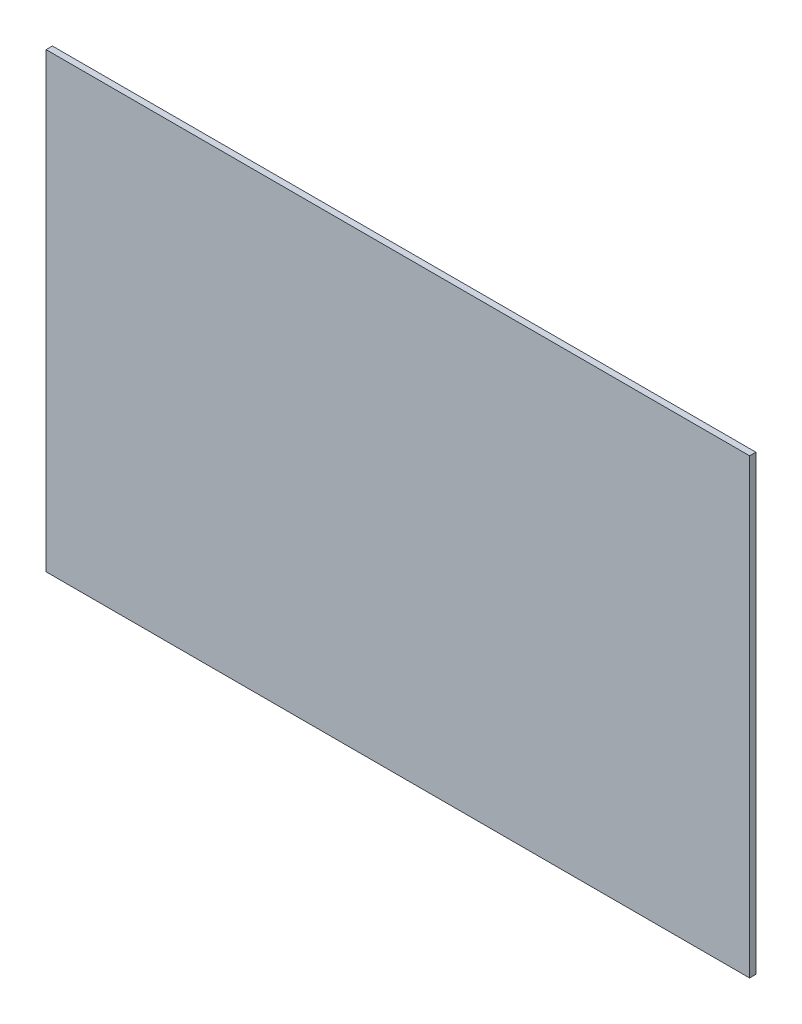
SolidWorks part; units mm, degrees
ref_plane "Front Plane" through (0, 0, 0) normal (0, 0, 1) x (1, 0, 0)
ref_plane "Top Plane" through (0, 0, 0) normal (0, 1, 0) x (1, 0, 0)
ref_plane "Right Plane" through (0, 0, 0) normal (1, 0, 0) x (0, 0, -1)
sketch "Sketch1" plane through (0, 0, 0) normal (0, 0, 1) x (1, 0, 0)
  line L1 (0, 0) -> (355.6, 0)
  line L2 (0, 0) -> (0, 228.6)
  line L3 (0, 228.6) -> (355.6, 228.6)
  line L4 (355.6, 0) -> (355.6, 228.6)
  dimension "D1" = 355.6
  dimension "D2" = 228.6
extrude "Boss-Extrude1" add sketch "Sketch1" along normal blind 3.175
